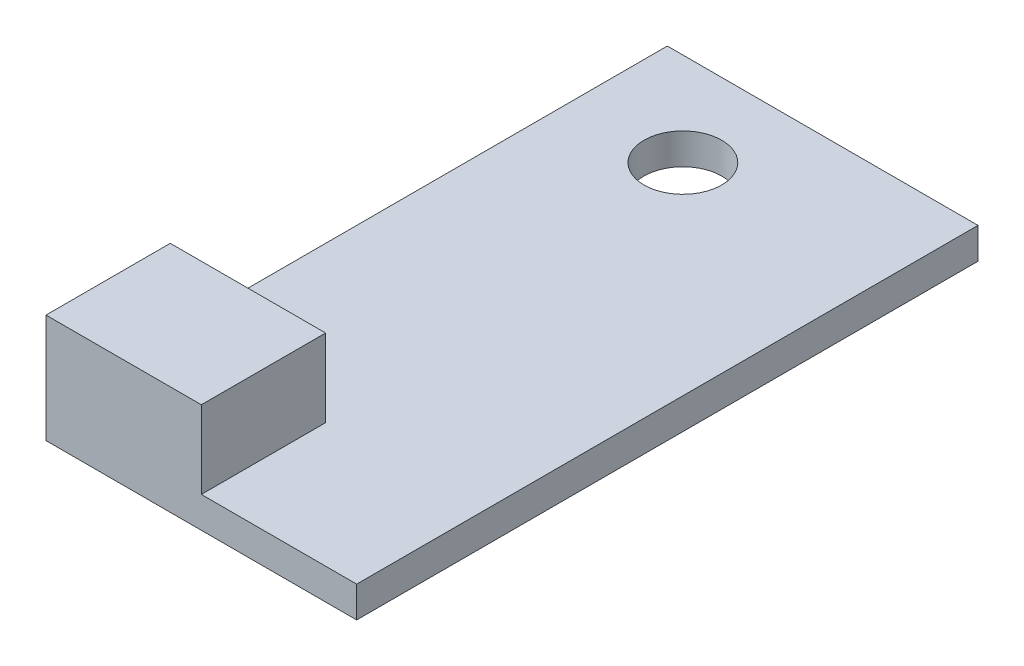
SolidWorks part; units mm, degrees
ref_plane "Front Plane" through (0, 0, 0) normal (0, 0, 1) x (1, 0, 0)
ref_plane "Top Plane" through (0, 0, 0) normal (0, 1, 0) x (1, 0, 0)
ref_plane "Right Plane" through (0, 0, 0) normal (1, 0, 0) x (0, 0, -1)
sketch "Sketch1" plane through (0, 0, 0) normal (0, 1, 0) x (1, 0, 0)
  line L1 (0, 0) -> (100, 0)
  line L2 (0, 0) -> (0, 200)
  line L3 (0, 200) -> (100, 200)
  line L4 (100, 0) -> (100, 200)
  dimension "D1" = 100
  dimension "D2" = 200
extrude "Boss-Extrude1" add sketch "Sketch1" along normal blind 10
sketch "Sketch2" plane through (0, 10, 0) normal (0, 1, 0) x (1, 0, 0)
  line L1 (0, 0) -> (50, 0)
  line L2 (0, 0) -> (0, 40)
  line L3 (0, 40) -> (50, 40)
  line L4 (50, 0) -> (50, 40)
  dimension "D1" = 50
  dimension "D2" = 40
extrude "Boss-Extrude2" add sketch "Sketch2" along normal blind 25
sketch "Sketch4" plane through (0, 10, 0) normal (0, 1, 0) x (1, 0, 0)
  line L0 (0, 200) -> (0, 40) construction
  line L1 (100, 200) -> (0, 200) construction
  circle A0 centre (35, 170) radius 12.5
  dimension "D1" = 25
  dimension "D2" = 35
  dimension "D3" = 30
extrude "Cut-Extrude1" cut sketch "Sketch4" against normal blind 25
